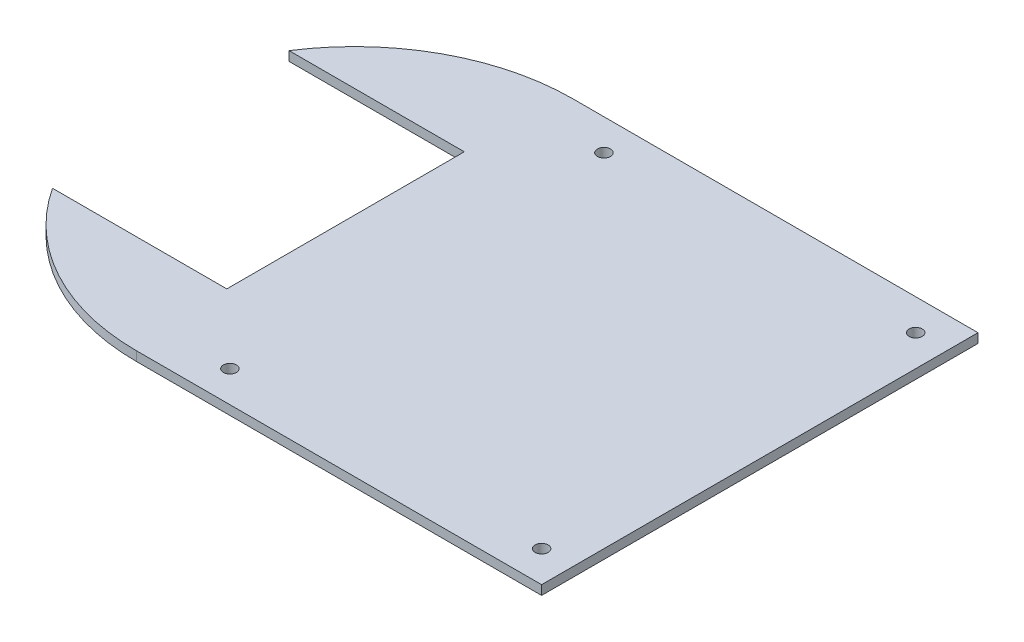
SolidWorks part; units mm, degrees
ref_plane "Front Plane" through (0, 0, 0) normal (0, 0, 1) x (1, 0, 0)
ref_plane "Top Plane" through (0, 0, 0) normal (0, 1, 0) x (1, 0, 0)
ref_plane "Right Plane" through (0, 0, 0) normal (1, 0, 0) x (0, 0, -1)
sketch "Sketch1" plane through (0, 0, 0) normal (0, 1, 0) x (1, 0, 0)
  line L0 (55, 64.1271) -> (55, -149.499) construction
  line L1 (65, -70) -> (-65, -70)
  line L2 (65, -70) -> (65, 70)
  line L3 (65, 70) -> (-65, 70)
  line L5 (65, -70) -> (-65, 70) construction
  line L6 (65, 70) -> (-65, -70) construction
  line L7 (-1000, 0) -> (49000, 0) construction
  line L8 (-123.5781, -38.3223) -> (-67.6637, -38.3223)
  line L9 (-67.6637, -38.3223) -> (-67.6637, 37.8582)
  line L10 (-67.6637, 37.8582) -> (-123.8792, 37.8582)
  line L12 (-176.6784, -37.3223) -> (-127.4717, -37.3223) construction
  line L14 (-127.325, 36.8582) -> (-176.8321, 36.8582) construction
  line L15 (-72.6637, -8.4263) -> (-72.6637, -17.1418) construction
  arc A0 (-65, -70) -> (-123.5781, -38.3223) centre (-65, 0) cw
  arc A1 (-123.8792, 37.8582) -> (-65, 70) centre (-65, 0) cw
  circle A2 centre (-44.9998, 59.9998) radius 2.1
  circle A3 centre (-44.9998, -60.0002) radius 2.1
  circle A4 centre (55.0002, 59.9998) radius 2.1
  circle A5 centre (55.0002, -60.0002) radius 2.1
  point P0 (0, 0)
  dimension "D7" = 4.2
  dimension "D1" = 140
  dimension "D2" = 130
  dimension "D3" = 10
  dimension "D4" = 1
  dimension "D5" = 5
  dimension "D6" = 1
extrude "Boss-Extrude1" add sketch "Sketch1" along normal blind 3
